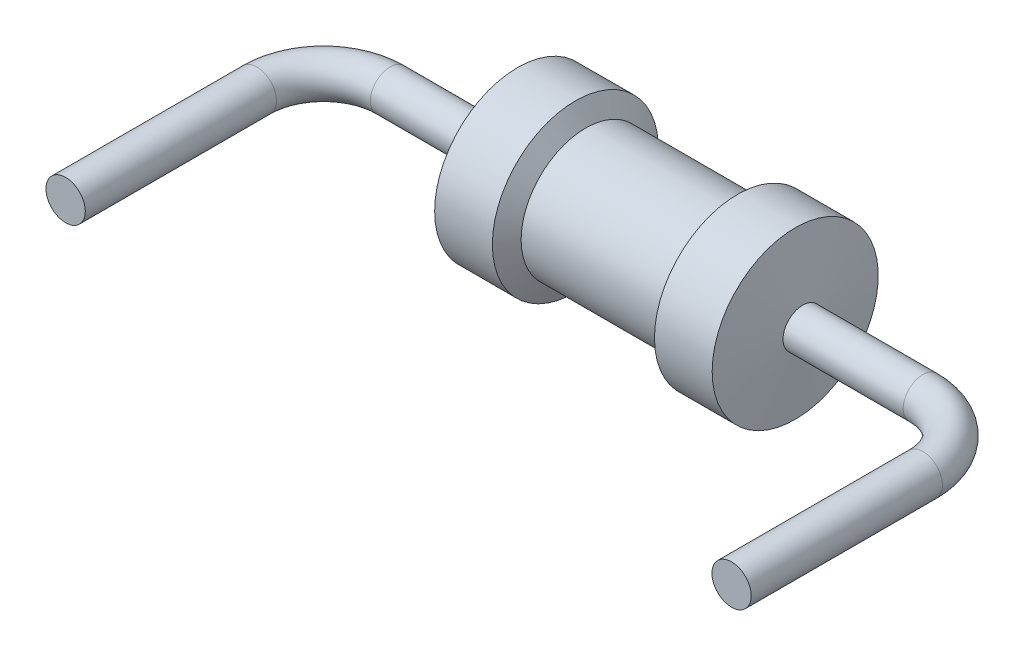
SolidWorks part; units mm, degrees
ref_plane "Front Plane" through (0, 0, 0) normal (0, 0, 1) x (1, 0, 0)
ref_plane "Top Plane" through (0, 0, 0) normal (0, 1, 0) x (1, 0, 0)
ref_plane "Right Plane" through (0, 0, 0) normal (1, 0, 0) x (0, 0, -1)
sketch "Sketch1" plane through (0, 0, 0) normal (0, 0, 1) x (1, 0, 0)
  line L0 (0, 0) -> (7.62, 0) construction
  line L1 (2.11, 0.95) -> (5.51, 0.95) construction
  line L2 (3.81, 0) -> (3.81, 6.1058) construction
  line L3 (2.11, 0) -> (2.2223, 0.95)
  line L4 (2.2223, 0.95) -> (2.8827, 0.95)
  line L5 (2.8827, 0.95) -> (3.0013, 0.7398)
  line L6 (5.51, 0) -> (5.3977, 0.95)
  line L7 (5.3977, 0.95) -> (4.7373, 0.95)
  line L8 (4.7373, 0.95) -> (4.6187, 0.7398)
  line L9 (4.6187, 0.7398) -> (3.0013, 0.7398)
  line L10 (2.11, 0) -> (5.51, 0)
  point P7 (3.81, 0.95)
  point P14 (3.81, 0.7398)
  dimension "D1" = 7.62
  dimension "D2" = 3.4
  dimension "D3" = 0.95
  dimension "D4" = 0.6604
  dimension "D5" = 0.6604
revolve "Revolve1" add sketch "Sketch1" angle 360 about L0
ref_plane "Plane1" through (0, 0, 0.95) normal (0, 0, 1) x (1, 0, 0)
ref_plane "Plane2" through (2.2223, 0, 0) normal (1, 0, 0) x (0, 0, -1)
ref_plane "Plane3" through (5.3977, 0, 0) normal (1, 0, 0) x (0, 0, -1)
ref_plane "Plane4" through (3.81, 0, 0) normal (1, 0, 0) x (0, 0, -1)
sketch "Sketch3" plane through (0, 0, 0) normal (0, 1, 0) x (1, 0, 0)
  line L0 (0, 0) -> (7.62, 0) construction
  line L1 (0, -0.95) -> (7.62, -0.95) construction
  line L2 (-1.045, -0.95) -> (1.045, -0.95) construction
  line L3 (2.2223, 0) -> (0.762, 0)
  line L5 (0, -0.762) -> (0, -0.95)
  line L6 (5.51, 0) -> (6.858, 0)
  line L7 (7.62, -0.762) -> (7.62, -0.95)
  line L9 (2.2223, -1.045) -> (2.2223, 1.045) construction
  line L10 (2.2223, 0) -> (5.51, 0)
  arc A0 (0, -0.762) -> (0.762, 0) centre (0.762, -0.762) cw
  arc A1 (7.62, -0.762) -> (6.858, 0) centre (6.858, -0.762) ccw
  dimension "D2" = 0.762
  dimension "D3" = 0.762
  dimension "D1" = 7.62
  dimension "D4" = 1.4603
  dimension "D5" = 0.188
sketch "Sketch4" plane through (2.2223, 0, 0) normal (1, 0, 0) x (0, 0, -1)
  circle A0 centre (0, 0) radius 0.225
  dimension "D1" = 0.45
ref_point "Point1"
sketch "Sketch5" plane through (0, 0, 0.95) normal (0, 0, 1) x (1, 0, 0)
  circle A0 centre (0, 0) radius 0.225
  dimension "D1" = 0.45
sweep "Sweep4" add profiles "Sketch5" path "Sketch3"
sketch "Sketch6" plane through (0, 0, 0.95) normal (0, 0, 1) x (1, 0, 0)
  circle A0 centre (0, 0) radius 0.225
  circle A1 centre (7.62, 0) radius 0.225
extrude "Boss-Extrude2" add sketch "Sketch6" along normal blind 2
